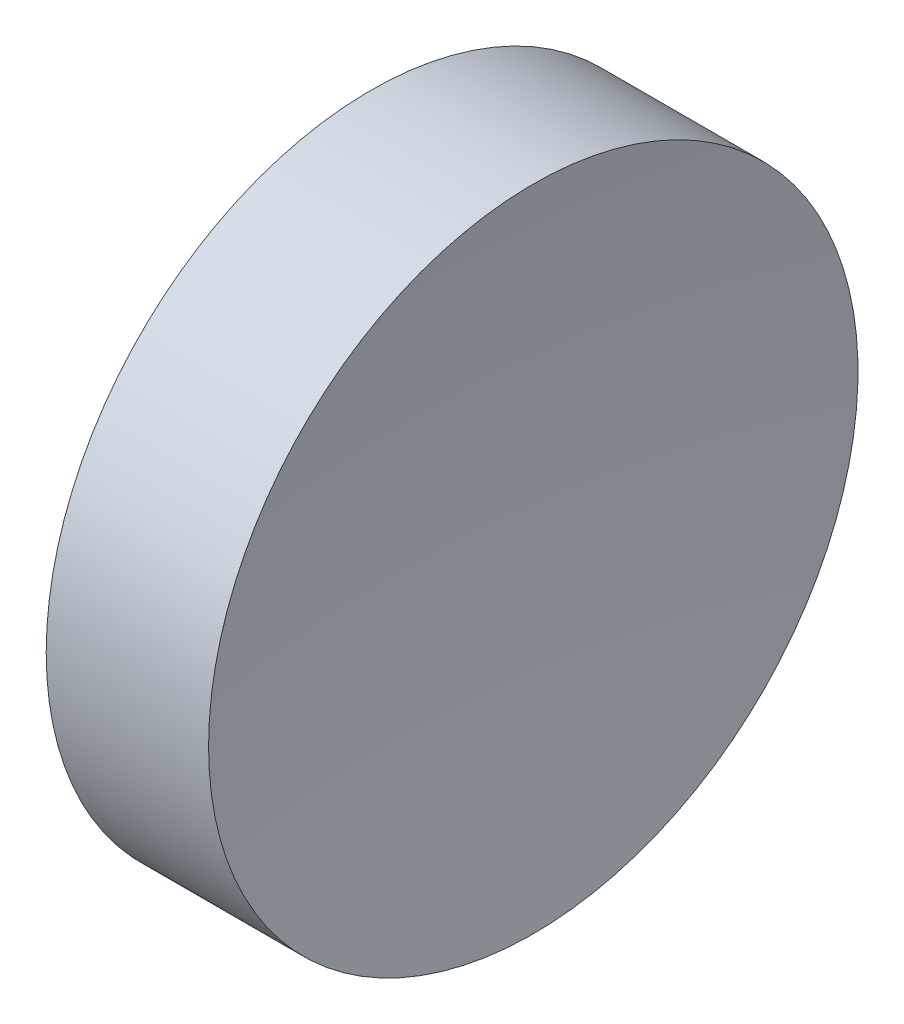
SolidWorks part; units mm, degrees
ref_plane "前视基准面" through (0, 0, 0) normal (0, 0, 1) x (1, 0, 0)
ref_plane "上视基准面" through (0, 0, 0) normal (0, 1, 0) x (1, 0, 0)
ref_plane "右视基准面" through (0, 0, 0) normal (1, 0, 0) x (0, 0, -1)
sketch "草图1" plane through (0, 0, 0) normal (0, 1, 0) x (1, 0, 0)
  line L0 (0, 0) -> (6.9328, 0) construction
  line L1 (0, 0) -> (5.54, 0)
  line L2 (0, 0) -> (0, 12.7)
  line L3 (0, 12.7) -> (6.3497, 12.7)
  arc A0 (6.3497, 12.7) -> (5.54, 0) centre (105.54, 0) ccw
  dimension "D3" = 100
  dimension "D1" = 5.54
  dimension "D2" = 12.7
revolve "旋转1" add sketch "草图1" angle 360 about L0
